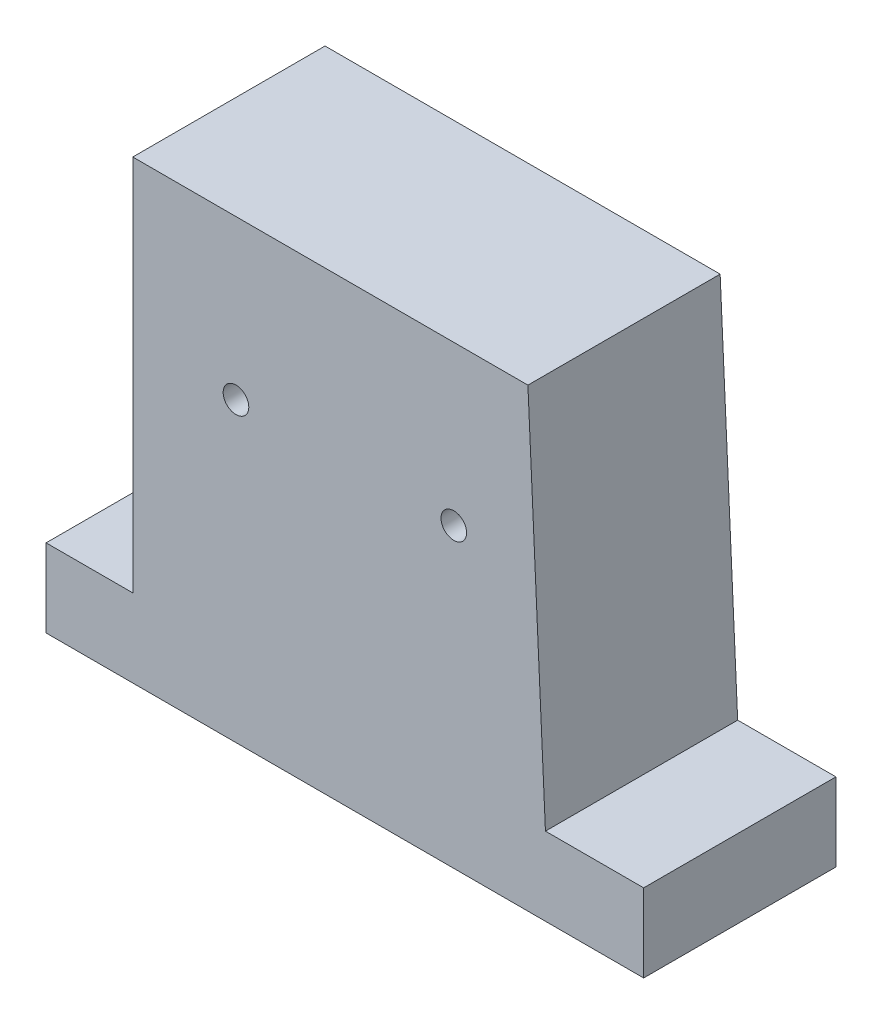
SolidWorks part; units mm, degrees
ref_plane "Front Plane" through (0, 0, 0) normal (0, 0, 1) x (1, 0, 0)
ref_plane "Top Plane" through (0, 0, 0) normal (0, 1, 0) x (1, 0, 0)
ref_plane "Right Plane" through (0, 0, 0) normal (1, 0, 0) x (0, 0, -1)
sketch "Sketch1" plane through (0, 0, 0) normal (0, 0, 1) x (1, 0, 0)
  line L0 (-78.4773, -6.7158) -> (-105.5344, -6.7158)
  line L2 (31.2766, -31.0847) -> (80.9737, -31.0847)
  line L3 (80.9737, -6.7158) -> (80.9737, -31.0847)
  line L4 (50.3153, -6.7158) -> (80.9737, -6.7158)
  line L5 (-105.5344, -6.7158) -> (-105.5344, -31.0847)
  line L6 (-55.8373, -31.0847) -> (-105.5344, -31.0847)
  line L7 (-78.4773, -6.7158) -> (-78.4773, 111.1057)
  line L8 (-78.4773, 111.1057) -> (44.8438, 111.1057)
  line L9 (-55.8373, -31.0847) -> (31.2766, -31.0847)
  line L10 (50.3153, -6.7158) -> (44.8438, 111.1057)
  circle A0 centre (-46.2714, 61.5865) radius 4
  circle A1 centre (21.7106, 61.5865) radius 4
extrude "Boss-Extrude1" add sketch "Sketch1" along normal blind 60
